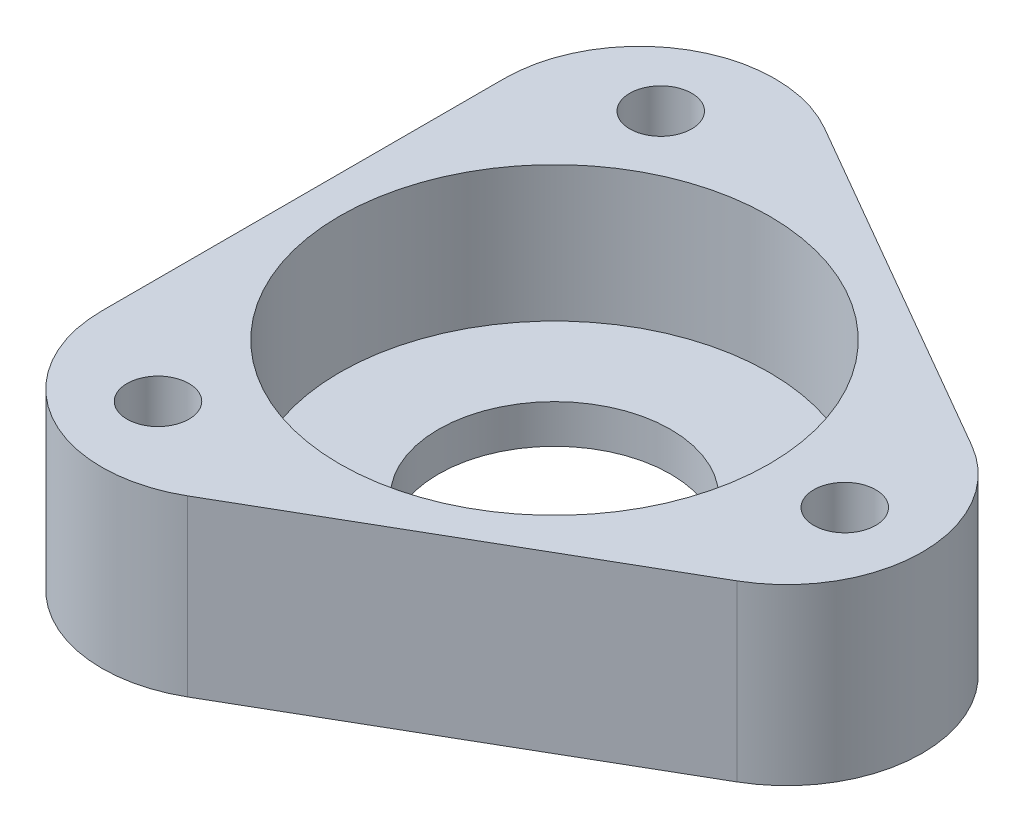
SolidWorks part; units mm, degrees
ref_plane "Front Plane" through (0, 0, 0) normal (0, 0, 1) x (1, 0, 0)
ref_plane "Top Plane" through (0, 0, 0) normal (0, 1, 0) x (1, 0, 0)
ref_plane "Right Plane" through (0, 0, 0) normal (1, 0, 0) x (0, 0, -1)
sketch "Sketch1" plane through (0, 0, 0) normal (0, 1, 0) x (1, 0, 0)
  line L0 (-13, 22.5167) -> (0, 0) construction
  line L1 (26, 0) -> (-13, 22.5167)
  line L2 (-13, 22.5167) -> (-13, -22.5167)
  line L3 (-13, -22.5167) -> (26, 0)
  circle A0 centre (0, 0) radius 13 construction
  circle A3 centre (-7.5, 12.9904) radius 1.6
  circle A4 centre (15, 0) radius 1.6
  circle A5 centre (-7.5, -12.9904) radius 1.6
  point P15 (0, 0)
  dimension "D1" = 26
  dimension "D2" = 15
  dimension "D4" = 3.2
  dimension "D3" = 3
extrude "Boss-Extrude1" add sketch "Sketch1" along normal blind 9
sketch "Sketch2" plane through (0, 9, 0) normal (0, 1, 0) x (1, 0, 0)
  circle A0 centre (0, 0) radius 11.1
  dimension "D1" = 22.2
extrude "Cut-Extrude1" cut sketch "Sketch2" against normal blind 7
fillet "Fillet1" radius 7 3 edges at (26, 4.5, 0) (-13, 4.5, 22.5167) (-13, 4.5, -22.5167)
sketch "Sketch3" plane through (0, 2, 0) normal (0, 1, 0) x (1, 0, 0)
  circle A0 centre (0, 0) radius 6
  dimension "D1" = 12
extrude "Cut-Extrude2" cut sketch "Sketch3" against normal through all
